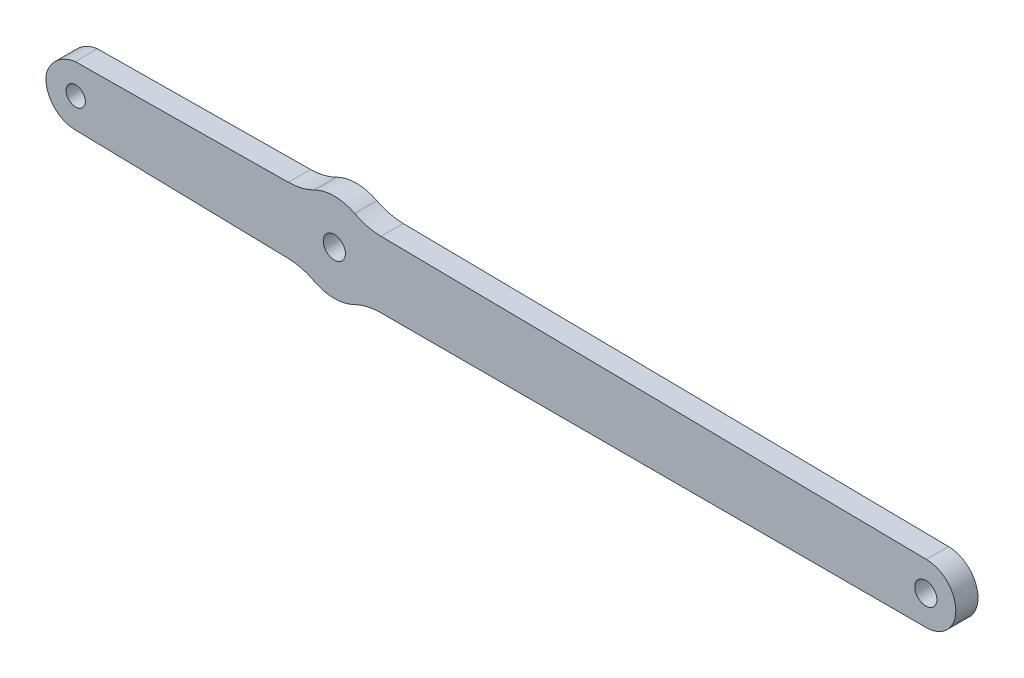
SolidWorks part; units mm, degrees
ref_plane "Front Plane" through (0, 0, 0) normal (0, 0, 1) x (1, 0, 0)
ref_plane "Top Plane" through (0, 0, 0) normal (0, 1, 0) x (1, 0, 0)
ref_plane "Right Plane" through (0, 0, 0) normal (1, 0, 0) x (0, 0, -1)
sketch "Model" plane through (0, 0, 0) normal (0, 0, 1) x (1, 0, 0)
  line L0 (67.0384, 41.4159) -> (104.0384, 41.4182)
  line L1 (56.5384, 41.4152) -> (67.0384, 41.4159)
  line L2 (46.0384, 41.4145) -> (56.5384, 41.4152)
  line L3 (34.7407, 41.4138) -> (46.0384, 41.4145)
  line L4 (-6.6022, 42.1684) -> (22.2082, 41.5169)
  line L5 (22.2663, 50.4432) -> (-6.5501, 50.1672)
  line L6 (108.5382, 49.4178) -> (34.7991, 50.3831)
  line L7 (104.0384, 41.4182) -> (108.5385, 41.4185)
  circle A0 centre (28.4875, 45.9394) radius 1.5
  circle A1 centre (108.4858, 45.4182) radius 1.5
  circle A2 centre (-6.4855, 46.1743) radius 1.3
  arc A3 (34.7407, 41.4138) -> (31.1677, 40.5713) centre (34.7414, 33.4132) ccw
  arc A4 (25.7189, 40.6163) -> (31.1677, 40.5713) centre (28.4875, 45.9394) ccw
  arc A5 (25.7189, 40.6163) -> (22.2082, 41.5169) centre (22.1436, 33.9725) ccw
  arc A6 (-10.4459, 46.8904) -> (-6.6022, 42.1684) centre (-6.5118, 46.1674) ccw
  arc A7 (-6.5501, 50.1672) -> (-10.4459, 46.8904) centre (-5.912, 45.4543) ccw
  arc A8 (22.2663, 50.4432) -> (25.7884, 51.298) centre (22.1856, 58.4595) ccw
  arc A9 (31.2373, 51.2721) -> (25.7884, 51.298) centre (28.4875, 45.9397) ccw
  arc A10 (31.2373, 51.2721) -> (34.7991, 50.3831) centre (34.904, 58.383) ccw
  arc A11 (108.5385, 41.4185) -> (108.5382, 49.4178) centre (108.5384, 45.4182) ccw
extrude "Boss-Extrude1" add sketch "Model" along normal blind 3
